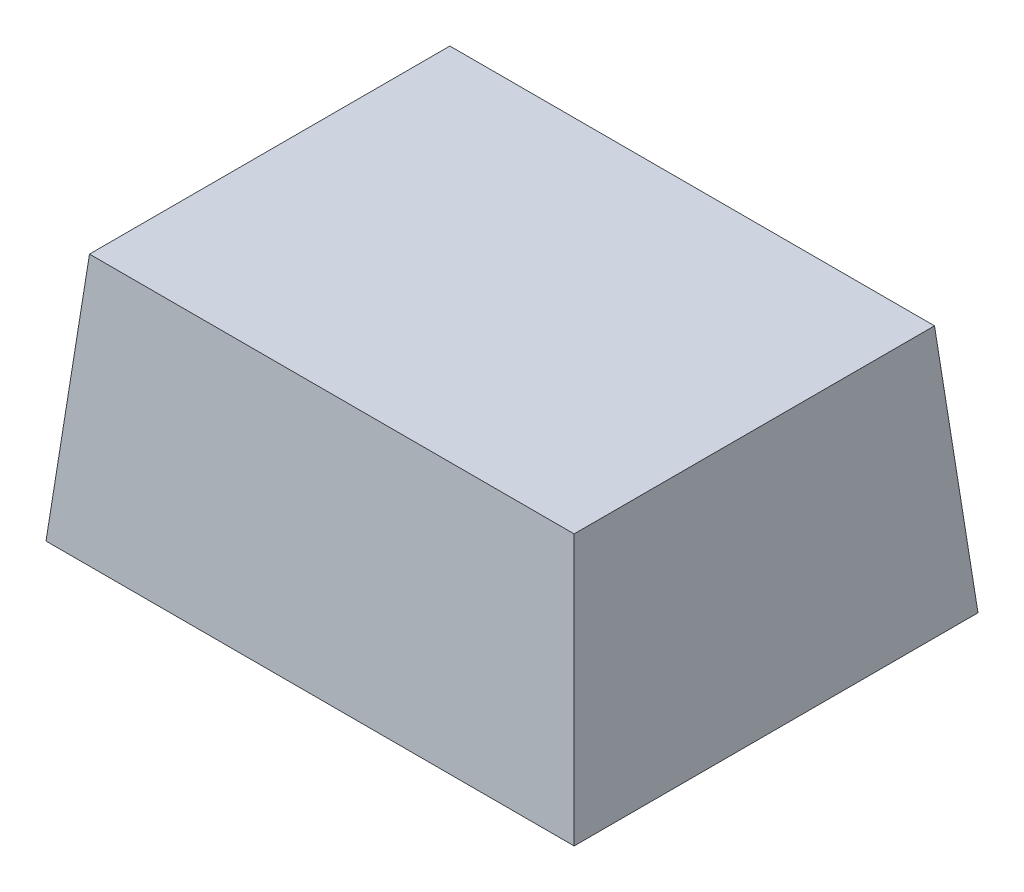
SolidWorks part; units mm, degrees
ref_plane "Front Plane" through (0, 0, 0) normal (0, 0, 1) x (1, 0, 0)
ref_plane "Top Plane" through (0, 0, 0) normal (0, 1, 0) x (1, 0, 0)
ref_plane "Right Plane" through (0, 0, 0) normal (1, 0, 0) x (0, 0, -1)
sketch "Sketch1" plane through (0, 0, 0) normal (0, 1, 0) x (1, 0, 0)
  line L1 (-0.425, -0.325) -> (0.425, -0.325)
  line L2 (-0.425, -0.325) -> (-0.425, 0.325)
  line L3 (-0.425, 0.325) -> (0.425, 0.325)
  line L4 (0.425, -0.325) -> (0.425, 0.325)
  line L5 (-0.425, -0.325) -> (0.425, 0.325) construction
  line L6 (-0.425, 0.325) -> (0.425, -0.325) construction
  point P0 (0, 0)
  dimension "D1" = 0.85
  dimension "D2" = 0.65
extrude "Boss-Extrude1" add sketch "Sketch1" along normal blind 0.4 draft 5
